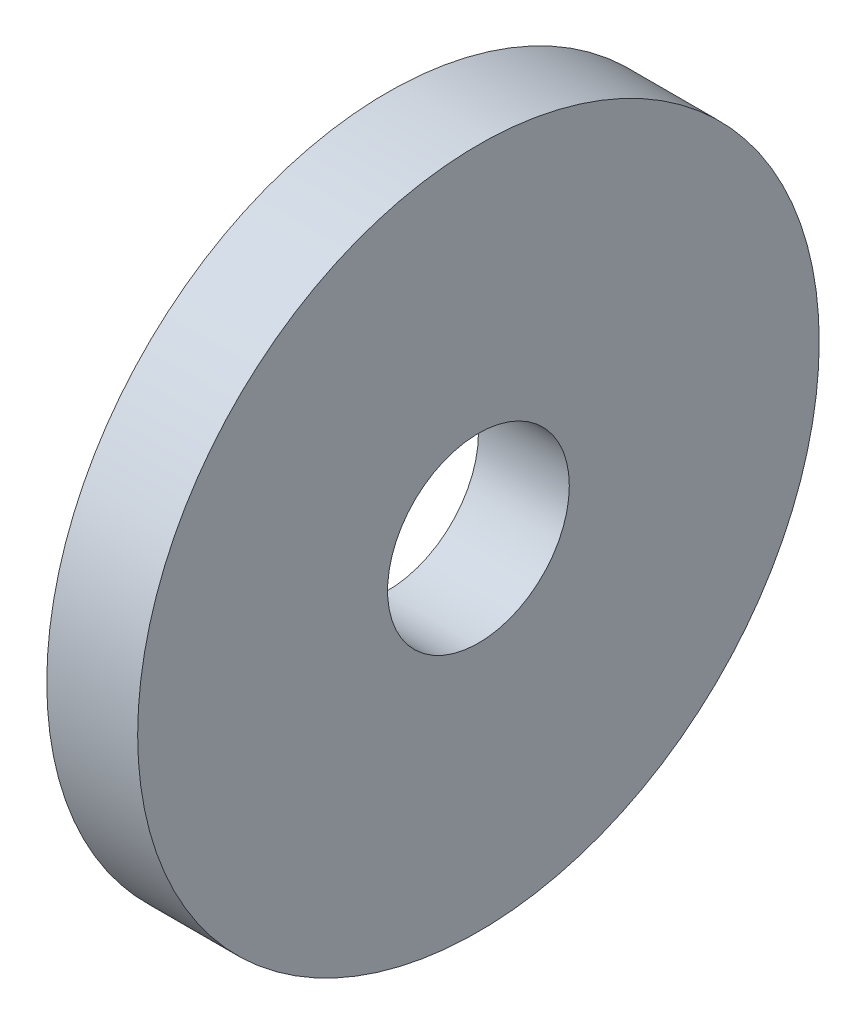
SolidWorks part; units mm, degrees
material "Thornel Mat VMA"
ref_plane "前视基准面" through (0, 0, 0) normal (0, 0, 1) x (1, 0, 0)
ref_plane "上视基准面" through (0, 0, 0) normal (0, 1, 0) x (1, 0, 0)
ref_plane "右视基准面" through (0, 0, 0) normal (1, 0, 0) x (0, 0, -1)
other "Configuration Table"
sketch "草图1" plane through (0, 0, 0) normal (1, 0, 0) x (0, 0, -1)
  circle A0 centre (0, 0) radius 7.5
  circle A1 centre (0, 0) radius 2
  dimension "D1" = 4
  dimension "D2" = 15
extrude "凸台-拉伸1" add sketch "草图1" along normal blind 2
